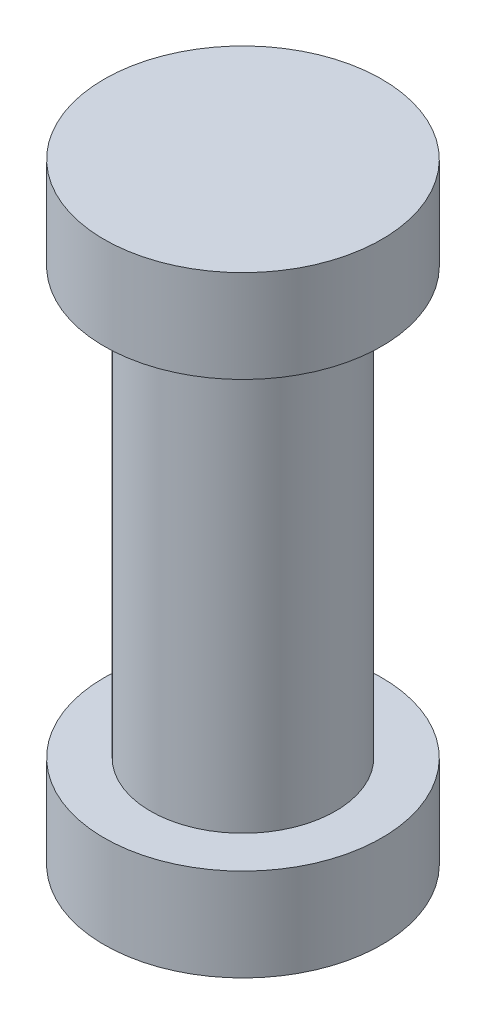
SolidWorks part; units mm, degrees
material "ABS"
ref_plane "Front Plane" through (0, 0, 0) normal (0, 0, 1) x (1, 0, 0)
ref_plane "Top Plane" through (0, 0, 0) normal (0, 1, 0) x (1, 0, 0)
ref_plane "Right Plane" through (0, 0, 0) normal (1, 0, 0) x (0, 0, -1)
sketch "Sketch1" plane through (0, 0, 0) normal (0, 0, 1) x (1, 0, 0)
  line L0 (0, 0) -> (9.525, 0)
  line L1 (9.525, 0) -> (9.525, 6.35)
  line L2 (9.525, 6.35) -> (6.3468, 6.35)
  line L3 (6.3468, 6.35) -> (6.3468, 35.56)
  line L4 (6.3468, 35.56) -> (9.525, 35.56)
  line L5 (9.525, 35.56) -> (9.525, 41.91)
  line L6 (9.525, 41.91) -> (0, 41.91)
  line L7 (0, 41.91) -> (0, 0)
  dimension "D1" = 6.35
  dimension "D2" = 6.35
  dimension "D3" = 9.525
  dimension "D4" = 6.3468
  dimension "D5" = 41.91
revolve "Revolve1" add sketch "Sketch1" angle 360 about L7
